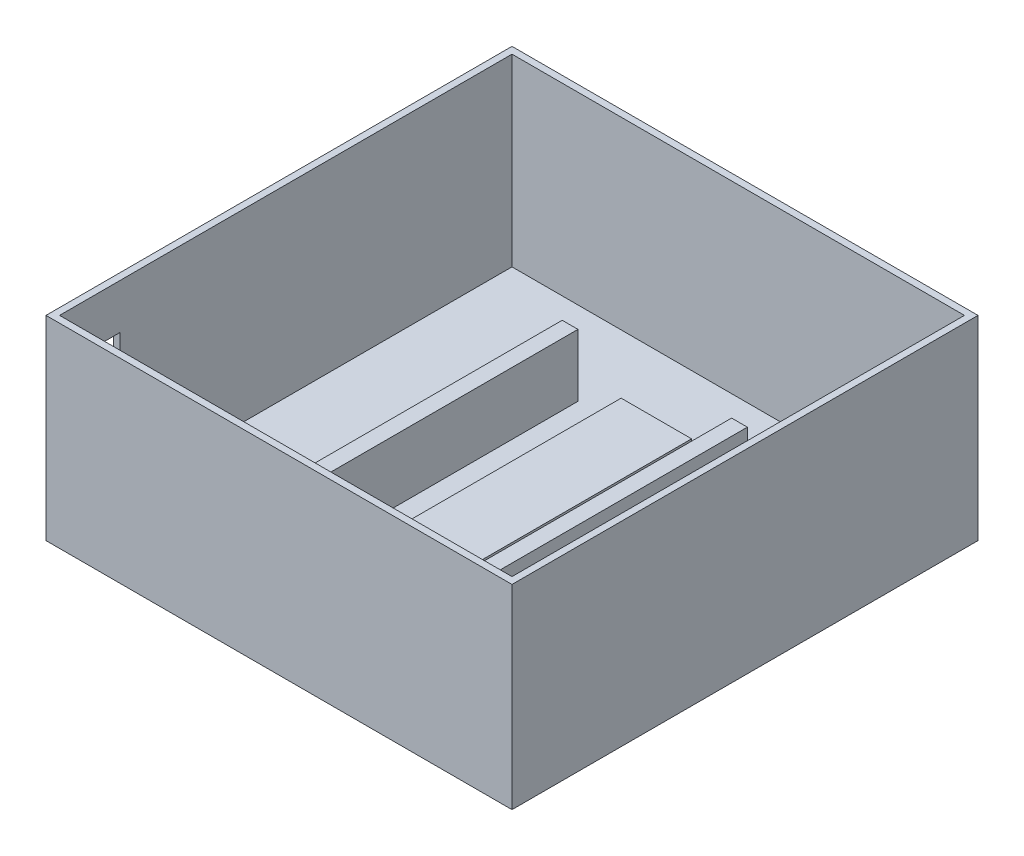
SolidWorks part; units mm, degrees
ref_plane "Front Plane" through (0, 0, 0) normal (0, 0, 1) x (1, 0, 0)
ref_plane "Top Plane" through (0, 0, 0) normal (0, 1, 0) x (1, 0, 0)
ref_plane "Right Plane" through (0, 0, 0) normal (1, 0, 0) x (0, 0, -1)
sketch "Sketch1" plane through (0, 0, 0) normal (0, 1, 0) x (1, 0, 0)
  line L1 (-43, 43) -> (43, 43)
  line L2 (-43, 43) -> (-43, -43)
  line L3 (-43, -43) -> (43, -43)
  line L4 (43, 43) -> (43, -43)
  line L5 (-43, 43) -> (43, -43) construction
  line L6 (-43, -43) -> (43, 43) construction
  point P0 (0, 0)
  dimension "D1" = 86
  dimension "D2" = 86
extrude "Boss-Extrude1" add sketch "Sketch1" along normal blind 36
sketch "Sketch3" plane through (0, 36, 0) normal (0, 1, 0) x (1, 0, 0)
  line L1 (-41.75, 41.75) -> (41.75, 41.75)
  line L2 (-41.75, 41.75) -> (-41.75, -41.75)
  line L3 (-41.75, -41.75) -> (41.75, -41.75)
  line L4 (41.75, 41.75) -> (41.75, -41.75)
  line L5 (-41.75, 41.75) -> (41.75, -41.75) construction
  line L6 (-41.75, -41.75) -> (41.75, 41.75) construction
  point P0 (0, 0)
  dimension "D1" = 83.5
  dimension "D2" = 83.5
extrude "Cut-Extrude1" cut sketch "Sketch3" against normal blind 34
sketch "Sketch4" plane through (0, 2, 0) normal (0, 1, 0) x (1, 0, 0)
  line L0 (-41.75, -41.75) -> (41.75, -41.75) construction
  line L1 (-6.5, 26.642) -> (6.5, 26.642)
  line L2 (-6.5, 26.642) -> (-6.5, -26.642)
  line L3 (-6.5, -26.642) -> (6.5, -26.642)
  line L4 (6.5, 26.642) -> (6.5, -26.642)
  line L5 (-6.5, 26.642) -> (6.5, -26.642) construction
  line L6 (-6.5, -26.642) -> (6.5, 26.642) construction
  point P0 (0, 0)
  dimension "D1" = 15.108
  dimension "D2" = 13
extrude "Boss-Extrude2" add sketch "Sketch4" along normal blind 4.2
sketch "Sketch5" plane through (0, 6.2, 0) normal (0, 1, 0) x (1, 0, 0)
  line L0 (-1000, 0) -> (49000, 0) construction
  line L1 (0, -1000) -> (0, 49000) construction
  line L2 (14.1781, -26.3515) -> (17.0834, -26.3515)
  line L3 (-14.1781, 26.3515) -> (-17.0834, 26.3515)
  line L4 (-14.1781, 26.3515) -> (-14.1781, -26.3515)
  line L5 (-14.1781, -26.3515) -> (-17.0834, -26.3515)
  line L6 (-17.0834, 26.3515) -> (-17.0834, -26.3515)
  line L7 (-14.1781, 26.3515) -> (-17.0834, -26.3515) construction
  line L8 (-14.1781, -26.3515) -> (-17.0834, 26.3515) construction
  line L9 (17.0834, 26.3515) -> (17.0834, -26.3515)
  line L10 (14.1781, 26.3515) -> (17.0834, 26.3515)
  line L11 (14.1781, 26.3515) -> (14.1781, -26.3515)
  line L13 (-6.5, 26.642) -> (-6.5, -26.642) construction
  point P4 (-15.6308, 0)
  dimension "D1" = 10.5834
extrude "Boss-Extrude4" add sketch "Sketch5" along normal blind 11.5 from surface at -4.2 separate body starting at face at (0, 2, 0)
sketch "Sketch7" plane through (-43, 0, 0) normal (-1, 0, 0) x (0, 0, 1)
  line L1 (30.5698, 27.6863) -> (38.5698, 27.6863)
  line L2 (30.5698, 27.6863) -> (30.5698, 17.1863)
  line L3 (30.5698, 17.1863) -> (38.5698, 17.1863)
  line L4 (38.5698, 27.6863) -> (38.5698, 17.1863)
  line L5 (30.5698, 27.6863) -> (38.5698, 17.1863) construction
  line L6 (30.5698, 17.1863) -> (38.5698, 27.6863) construction
  point P0 (34.5698, 22.4363)
  dimension "D1" = 10.5
  dimension "D2" = 8
extrude "Cut-Extrude2" cut sketch "Sketch7" against normal blind 2
